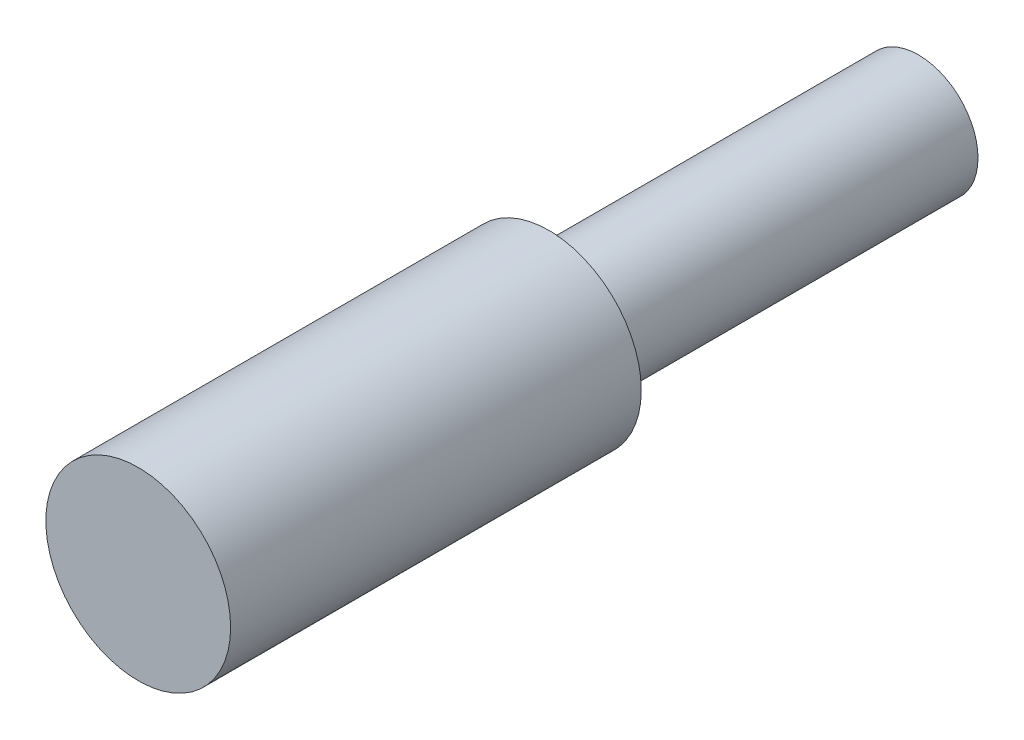
SolidWorks part; units mm, degrees
ref_plane "Front Plane" through (0, 0, 0) normal (0, 0, 1) x (1, 0, 0)
ref_plane "Top Plane" through (0, 0, 0) normal (0, 1, 0) x (1, 0, 0)
ref_plane "Right Plane" through (0, 0, 0) normal (1, 0, 0) x (0, 0, -1)
sketch "Sketch1" plane through (0, 0, 0) normal (0, 0, 1) x (1, 0, 0)
  circle A0 centre (0, 0) radius 2.25
  circle A1 centre (0, 0) radius 3.975
  dimension "D1" = 4.5
  dimension "D2" = 7.95
sketch "Sketch2" plane through (0, 0, 0) normal (0, 0, 1) x (1, 0, 0)
  circle A0 centre (0, 0) radius 2.25 construction
  circle A1 centre (0, 0) radius 2.25
extrude "Boss-Extrude1" add sketch "Sketch2" along normal blind 10
sketch "Sketch3" plane through (0, 0, 0) normal (0, 0, -1) x (-1, 0, 0)
  circle A0 centre (0, 0) radius 1.45
  dimension "D1" = 2.9
extrude "Boss-Extrude2" add sketch "Sketch3" along normal blind 9
sketch "Sketch4" plane through (0, 0, 10) normal (0, 0, 1) x (1, 0, 0)
  point P0 (0, 0)
